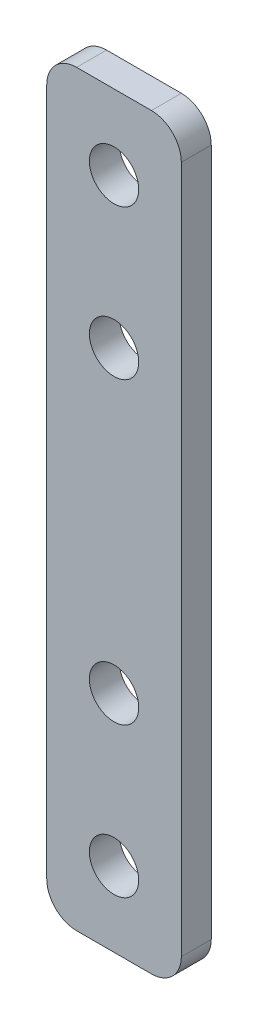
SolidWorks part; units mm, degrees
material "Простая углеродистая сталь"
ref_plane "Спереди" through (0, 0, 0) normal (0, 0, 1) x (1, 0, 0)
ref_plane "Сверху" through (0, 0, 0) normal (0, 1, 0) x (1, 0, 0)
ref_plane "Сбоку" through (0, 0, 0) normal (1, 0, 0) x (0, 0, -1)
sketch "Эскиз1" plane through (0, 0, 0) normal (0, 0, 1) x (1, 0, 0)
  line L1 (-4.5, -25) -> (4.5, -25)
  line L2 (-4.5, -25) -> (-4.5, 25)
  line L3 (-4.5, 25) -> (4.5, 25)
  line L4 (4.5, -25) -> (4.5, 25)
  line L5 (-4.5, -25) -> (4.5, 25) construction
  line L6 (-4.5, 25) -> (4.5, -25) construction
  point P0 (0, 0)
  dimension "D1" = 50
  dimension "D2" = 9
extrude "Бобышка-Вытянуть1" add sketch "Эскиз1" along normal blind 2
hole_wizard "Отверстие обработанное метчиком M41" positions "Эскиз2" profile "Эскиз3" tap size "M4" standard "DIN"
sketch "Эскиз2" plane through (0, 0, 2) normal (0, 0, 1) x (1, 0, 0)
  line L6 (0, -25) -> (0, 25) construction
  line L7 (-4.5, -25) -> (4.5, -25) construction
  line L8 (4.5, 25) -> (-4.5, 25) construction
  point P29 (0, 20)
  point P31 (0, 10)
  point P33 (0, -20)
  point P35 (0, -10)
  dimension "D1" = 5
  dimension "D2" = 5
  dimension "D3" = 10
  dimension "D4" = 10
sketch "Эскиз3" plane through (0, -10, 2) normal (1, 0, 0) x (0, -1, 0)
  line L0 (0, 0) -> (0, 12.4914)
  line L1 (0, 12.4914) -> (1.65, 11.5)
  line L2 (1.65, 11.5) -> (1.65, 0)
  line L5 (1.65, 0) -> (0, 0)
  line L10 (0, 12.4914) -> (-1.65, 11.5) construction
  line L11 (0, -6.35) -> (0, 107.95) construction
  dimension "Диаметр сверла" = 3.3
  dimension "Глубина сверла" = 11.5
  dimension "Угол заточки сверла" = 118
cosmetic thread "Отверстие резьбы1"
cosmetic thread "Отверстие резьбы2"
cosmetic thread "Отверстие резьбы3"
cosmetic thread "Отверстие резьбы4"
fillet "Скругление1" radius 2 4 edges at (-4.5, -25, 1) (4.5, -25, 1) (4.5, 25, 1) (-4.5, 25, 1)
